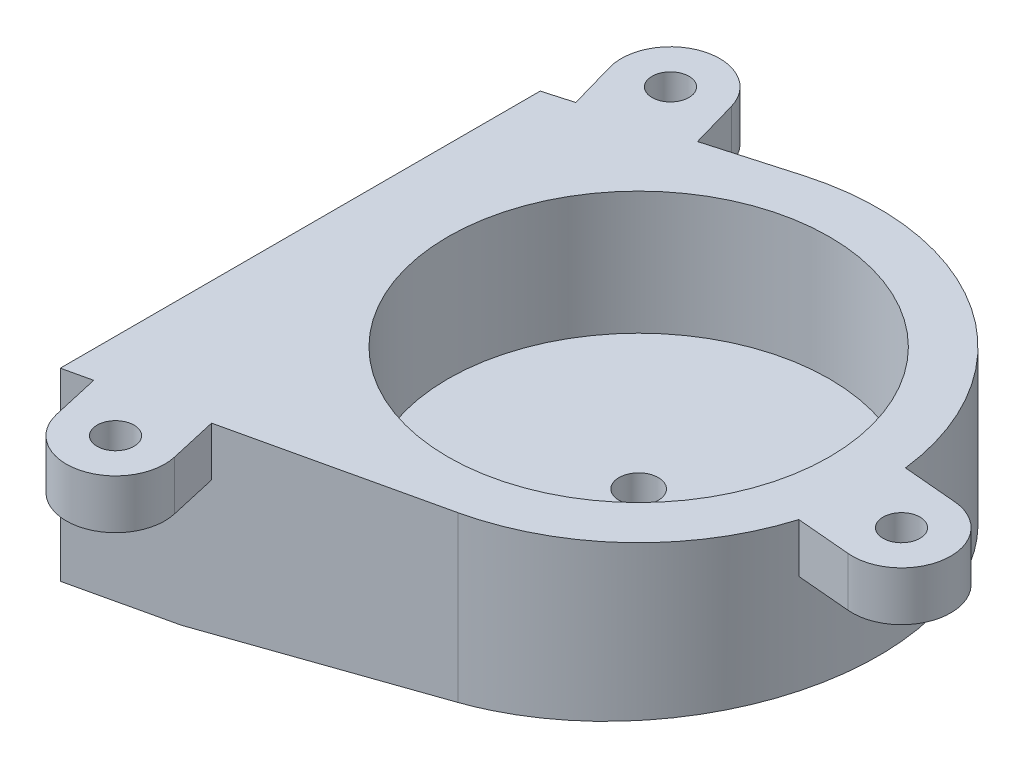
SolidWorks part; units mm, degrees
ref_plane "Front" through (0, 0, 0) normal (0, 0, 1) x (1, 0, 0)
ref_plane "Top" through (0, 0, 0) normal (0, 1, 0) x (1, 0, 0)
ref_plane "Right" through (0, 0, 0) normal (1, 0, 0) x (0, 0, -1)
sketch "Sketch1" plane through (0, 0, 0) normal (0, 1, 0) x (1, 0, 0)
  circle A0 centre (0, 0) radius 15.5
  dimension "D1" = 31
extrude "Boss-Extrude1" add sketch "Sketch1" along normal blind 5
sketch "Sketch2" plane through (0, 0, 0) normal (0, -1, 0) x (1, 0, 0)
  line L0 (4.3235, 19.0147) -> (-22, 25)
  line L1 (-22, 25) -> (-22, -14)
  line L2 (-22, -14) -> (-5.3514, -18.7513)
  circle A3 centre (0, 0) radius 19.5
  arc A4 (-5.3514, -18.7513) -> (4.3235, 19.0147) centre (0, 0) ccw
  circle M5 centre (0, 0) radius 15.5
  dimension "D4" = 14
  dimension "D2" = 22
  dimension "D3" = 39
  dimension "D1" = 4
extrude "Boss-Extrude2" add sketch "Sketch2" against normal blind 15 contours L2 A4 L0 L1 M5
sketch "Sketch17" plane through (0, 0, 0) normal (0, 0, 1) x (1, 0, 0)
  line L0 (-22, 0) -> (-14, 0)
  line L1 (4.3235, 0) -> (-22, 0) construction
  line L2 (-14, 0) -> (19.5, 3)
  line L3 (19.5, 0) -> (19.5, 15) construction
  line L4 (19.5, 3) -> (19.5, 0)
  line L5 (19.5, 0) -> (-14, 0)
  line L6 (19.5, 15) -> (-5.3514, 15) construction
  dimension "D1" = 8
  dimension "D2" = 12
extrude "Cut-Extrude7" cut sketch "Sketch17" against normal through all and the other way through all contours L5 L4 L2
sketch "Sketch18" plane through (0, 5, 0) normal (0, 1, 0) x (1, 0, 0)
  circle A0 centre (0, 0) radius 1.6
  dimension "D1" = 3.2
extrude "Cut-Extrude8" cut sketch "Sketch18" against normal through all contours A0
sketch "Sketch19" plane through (0, 0, 0) normal (0, -1, 0) x (1, 0, 0)
  line L0 (-22, 5.5) -> (-18, 5.5) construction
  line L1 (-22, 25) -> (-22, -14) construction
  circle A0 centre (-18, 5.5) radius 2.05
  dimension "D2" = 4.1
  dimension "D1" = 4
extrude "Cut-Extrude9" cut sketch "Sketch19" against normal blind 6
ref_plane "Plane5" through (0, 2, 0) normal (0, 1, 0) x (1, 0, 0)
sketch "Sketch20" plane through (0, 2, 0) normal (0, 1, 0) x (1, 0, 0)
  circle A0 centre (0, 0) radius 4
  dimension "D1" = 8
extrude "Cut-Extrude10" cut sketch "Sketch20" against normal up to next
sketch "Sketch21" plane through (0, 15, 0) normal (0, 1, 0) x (1, 0, 0)
  line L0 (-22, 14) -> (-5.3514, 18.7513) construction
  line L1 (-22, -25) -> (-22, 14) construction
  line L2 (-20.8464, 18.4889) -> (-19.7487, 14.6425)
  line L3 (-13.1536, 20.6844) -> (-12.0558, 16.838)
  line L4 (4.3235, -19.0147) -> (-22, -25) construction
  line L5 (-18.9004, -28.3973) -> (-19.7873, -24.4969)
  line L6 (-11.0996, -26.6236) -> (-11.9864, -22.7232)
  line L7 (0, 0) -> (15.5, 0) construction
  line L8 (18.6641, -5.6482) -> (23.062, -6.0329)
  line L9 (19.3613, 2.3214) -> (23.7592, 1.9366)
  line L10 (0, 0) -> (23.4106, -2.0482) construction
  line L11 (0.3486, 3.9848) -> (23.7592, 1.9366) construction
  line L12 (-0.3486, -3.9848) -> (23.062, -6.0329) construction
  line L13 (-17, 19.5867) -> (-15, -27.5105) construction
  line L14 (23.4106, -2.0482) -> (-16.0102, -3.7222) construction
  arc A0 (-13.1536, 20.6844) -> (-20.8464, 18.4889) centre (-17, 19.5867) ccw
  circle A1 centre (-17, 19.5867) radius 1.5
  arc A2 (-18.9004, -28.3973) -> (-11.0996, -26.6236) centre (-15, -27.5105) ccw
  circle A3 centre (-15, -27.5105) radius 1.5
  circle A4 centre (23.4106, -2.0482) radius 4
  circle A5 centre (23.4106, -2.0482) radius 1.5
  circle A6 centre (0, 0) radius 15.5 construction
  arc A7 (4.3235, -19.0147) -> (-5.3514, 18.7513) centre (0, 0) ccw construction
  arc A8 (18.6641, -5.6482) -> (19.3613, 2.3214) centre (0, 0) ccw
  line M14 (-5.3514, 18.7513) -> (-22, 14)
  line M16 (-22, -25) -> (4.3235, -19.0147)
  arc M17 (4.3235, -19.0147) -> (-5.3514, 18.7513) centre (0, 0) ccw
  dimension "D1" = 8
  dimension "D3" = 3
  dimension "D5" = 8
  dimension "D6" = 3
  dimension "D9" = 8
  dimension "D10" = 3
  dimension "D2" = 4
  dimension "D4" = 5
  dimension "D7" = 4
  dimension "D8" = 7
  dimension "D11" = 23.5
  dimension "D12" = 5
  dimension "D13" = 4
  dimension "D14" = 4
extrude "Boss-Extrude3" add sketch "Sketch21" against normal blind 4 contours L3 A0 L2 A1 M14 | L5 A2 L6 A3 M16 | A4 L8 M17 | A4 A5 | A4 L9 M17
